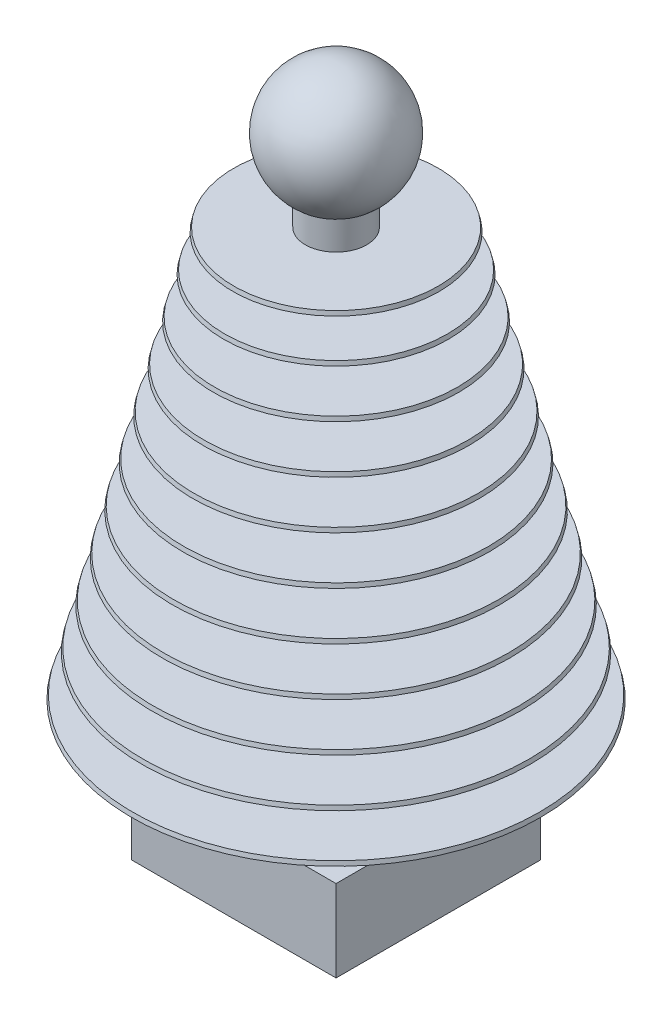
SolidWorks part; units mm, degrees
ref_plane "Front Plane" through (0, 0, 0) normal (0, 0, 1) x (1, 0, 0)
ref_plane "Top Plane" through (0, 0, 0) normal (0, 1, 0) x (1, 0, 0)
ref_plane "Right Plane" through (0, 0, 0) normal (1, 0, 0) x (0, 0, -1)
ref_axis "Axis1" through (0, -55, 0) along (0, 1, 0)
sketch "Sketch1" plane through (0, 0, 0) normal (0, 0, 1) x (1, 0, 0)
  line L0 (0, 50) -> (25, 50)
  line L1 (0, -55) -> (0, 55) construction
  line L2 (25, 50) -> (25.25, 49)
  line L3 (50, -50) -> (0, -50)
  line L4 (0, -50) -> (0, 50) construction
  line L5 (0, -49) -> (49.75, -49)
  line L6 (0, -39) -> (47.25, -39)
  line L7 (47.5, -40) -> (0, -40)
  line L8 (0, -29) -> (44.75, -29)
  line L9 (45, -30) -> (0, -30)
  line L10 (0, -19) -> (42.25, -19)
  line L11 (42.5, -20) -> (0, -20)
  line L12 (0, -9) -> (39.75, -9)
  line L13 (40, -10) -> (0, -10)
  line L14 (0, 1) -> (37.25, 1)
  line L15 (37.5, 0) -> (0, 0)
  line L16 (0, 11) -> (34.75, 11)
  line L17 (35, 10) -> (0, 10)
  line L18 (0, 21) -> (32.25, 21)
  line L19 (32.5, 20) -> (0, 20)
  line L20 (0, 31) -> (29.75, 31)
  line L21 (30, 30) -> (0, 30)
  line L22 (0, 41) -> (27.25, 41)
  line L23 (27.5, 40) -> (0, 40)
  line L24 (49.75, -49) -> (50, -50)
  line L25 (47.25, -39) -> (47.5, -40)
  line L26 (0, 51) -> (36.9107, 51) [skipped]
  line L27 (50, 50) -> (0, 50) [skipped]
  line L28 (44.75, -29) -> (45, -30)
  line L29 (42.25, -19) -> (42.5, -20)
  line L30 (39.75, -9) -> (40, -10)
  line L31 (37.25, 1) -> (37.5, 0)
  line L32 (34.75, 11) -> (35, 10)
  line L33 (32.25, 21) -> (32.5, 20)
  line L34 (29.75, 31) -> (30, 30)
  line L35 (25.25, 49) -> (0, 49)
  line L36 (27.25, 41) -> (27.5, 40)
  line L37 (0, 50) -> (0, 49)
  line L38 (0, 41) -> (0, 40)
  line L39 (0, 31) -> (0, 30)
  line L40 (0, 21) -> (0, 20)
  line L41 (0, 11) -> (0, 10)
  line L42 (0, 1) -> (0, 0)
  line L43 (0, -9) -> (0, -10)
  line L44 (0, -19) -> (0, -20)
  line L45 (0, -29) -> (0, -30)
  line L46 (0, -39) -> (0, -40)
  line L47 (0, -49) -> (0, -50)
  point P6 (0, 0)
  dimension "D1" = 100
  dimension "D2" = 25
  dimension "D3" = 50
  dimension "D4" = 1
  dimension "D6" = 10
  dimension "D7" = 1
  dimension "D5" = 11
revolve "Revolve1" add sketch "Sketch1" angle 360 about L4
sketch "Sketch2" plane through (0, -49, 0) normal (0, 1, 0) x (1, 0, 0)
  circle A0 centre (0, 0) radius 7.5
  dimension "D1" = 15
extrude "Boss-Extrude1" add sketch "Sketch2" along normal offset from surface 10 and the other way blind 15 up to face at (25, 50, 0) offset beyond the face yes
sketch "Sketch3" plane through (0, 0, 0) normal (0, 0, 1) x (1, 0, 0)
  line L0 (7.5, 60) -> (-7.5, 60) construction
  line L1 (0, 85) -> (0, 55)
  line L2 (0, -55) -> (0, 55) construction
  arc A0 (0, 85) -> (0, 55) centre (0, 70) cw
  point P7 (0, 85)
  point P8 (0, 0)
  point P9 (0, 0)
  dimension "D2" = 15
  dimension "D1" = 10
revolve "Revolve2" add sketch "Sketch3" angle 360 about axis through (0, -55, 0) along (0, 1, 0)
sketch "Sketch4" plane through (0, -64, 0) normal (0, -1, 0) x (1, 0, 0)
  line L1 (-25, 25) -> (25, 25)
  line L2 (-25, 25) -> (-25, -25)
  line L3 (-25, -25) -> (25, -25)
  line L4 (25, 25) -> (25, -25)
  line L5 (-25, 25) -> (25, -25) construction
  line L6 (-25, -25) -> (25, 25) construction
  point P0 (0, 0)
  dimension "D1" = 50
  dimension "D2" = 50
extrude "Boss-Extrude2" add sketch "Sketch4" along normal blind 20
